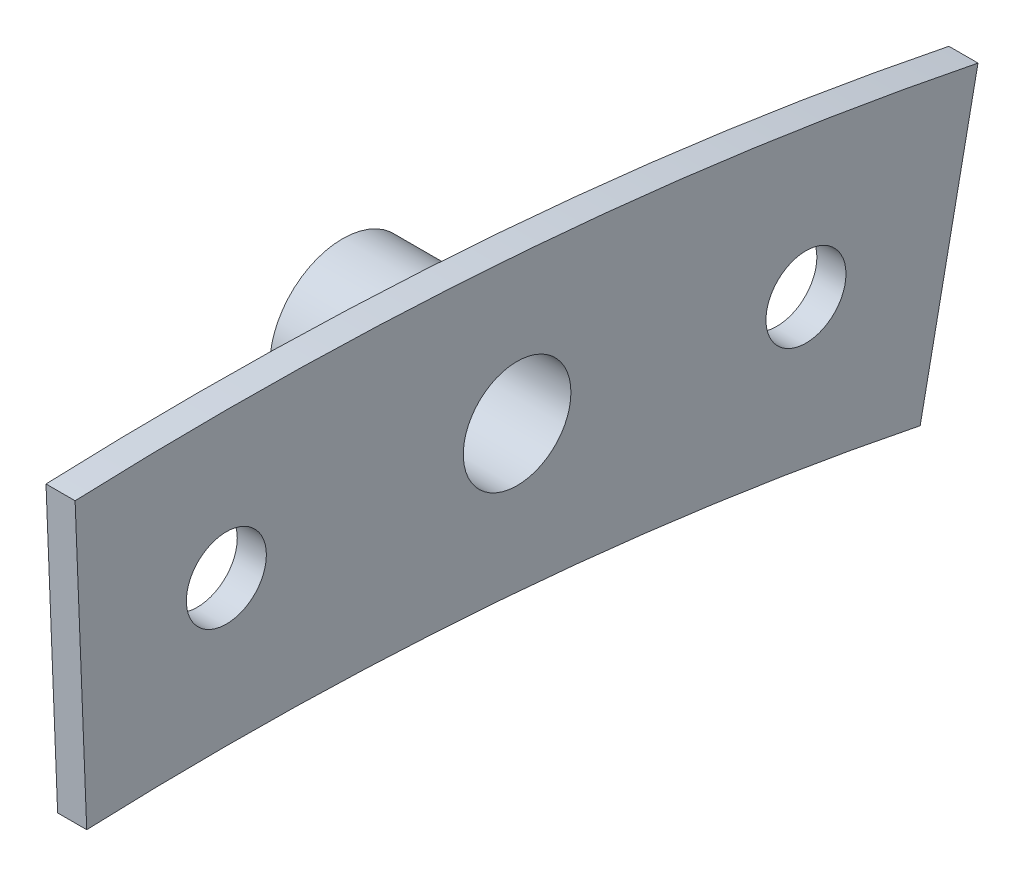
SolidWorks part; units mm, degrees
ref_plane "Front Plane" through (0, 0, 0) normal (0, 0, 1) x (1, 0, 0)
ref_plane "Top Plane" through (0, 0, 0) normal (0, 1, 0) x (1, 0, 0)
ref_plane "Right Plane" through (0, 0, 0) normal (1, 0, 0) x (0, 0, -1)
sketch "Sketch1" plane through (0, 0, 0) normal (1, 0, 0) x (0, 0, -1)
  line L0 (-12.1896, 304.5562) -> (-13.2054, 329.9358)
  line L1 (0, 317.5) -> (0, 0) construction
  line L2 (60.568, 298.7215) -> (65.6153, 323.615)
  line L3 (65.6153, 323.615) -> (0, 0) construction
  arc A0 (0, 317.5) -> (50.5969, 313.4425) centre (0, 0) cw
  circle A1 centre (0, 317.5) radius 3.4925
  circle A2 centre (25.3797, 316.484) radius 4.699
  circle A3 centre (50.5969, 313.4425) radius 3.4925
  arc A4 (-12.1896, 304.5562) -> (60.568, 298.7215) centre (0, 0) cw
  arc A5 (-13.2054, 329.9358) -> (65.6153, 323.615) centre (0, 0) cw
  point P5 (25.3797, 316.484)
  point P13 (-12.6975, 317.246)
  point P15 (63.0916, 311.1683)
  dimension "D1" = 317.5
  dimension "D3" = 6.985
  dimension "D4" = 9.398
  dimension "D5" = 6.985
  dimension "D6" = 304.8
  dimension "D7" = 25.4
  dimension "D8" = 12.6975
  dimension "D2" = 25.4
  dimension "D9" = 12.7
extrude "Boss-Extrude1" add sketch "Sketch1" along normal blind 2.54
sketch "Sketch2" plane through (0, 0, 0) normal (-1, 0, 0) x (0, 0, 1)
  circle A0 centre (-25.3797, 316.484) radius 6.35
  dimension "D1" = 12.7
extrude "Boss-Extrude2" add sketch "Sketch2" along normal blind 12.7 contours A0
sketch "Sketch4" plane through (0, 0, 0) normal (1, 0, 0) x (0, 0, -1)
  circle A0 centre (25.3797, 316.484) radius 4.699
  dimension "D1" = 9.398
extrude "Cut-Extrude1" cut sketch "Sketch4" against normal blind 6.35
